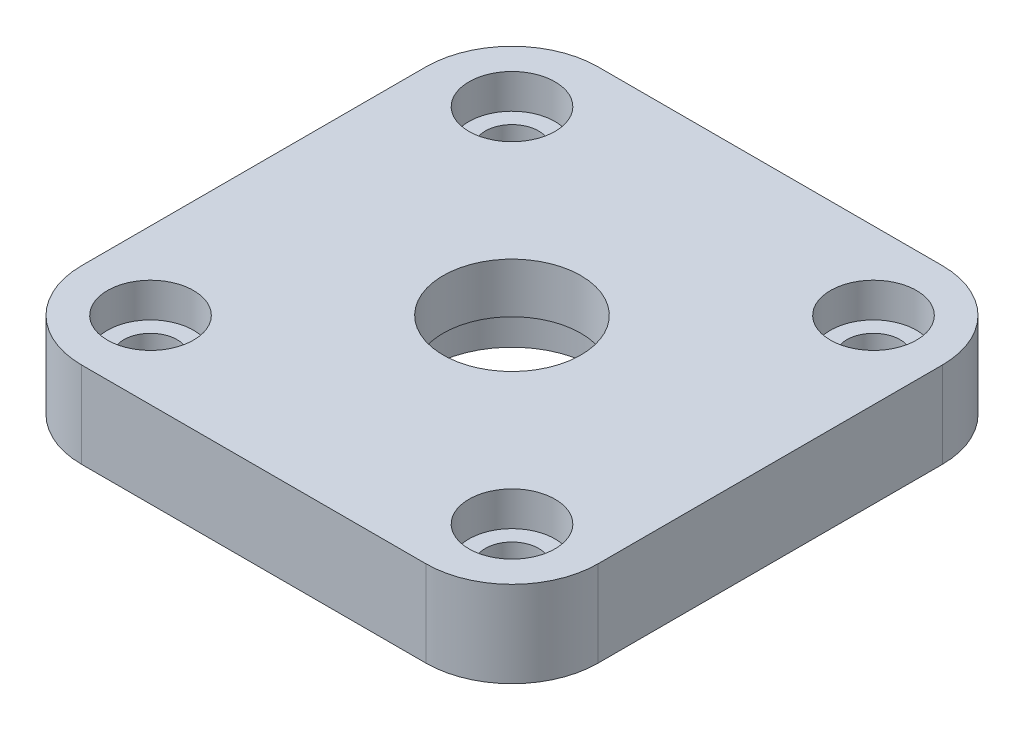
SolidWorks part; units mm, degrees
ref_plane "Front Plane" through (0, 0, 0) normal (0, 0, 1) x (1, 0, 0)
ref_plane "Top Plane" through (0, 0, 0) normal (0, 1, 0) x (1, 0, 0)
ref_plane "Right Plane" through (0, 0, 0) normal (1, 0, 0) x (0, 0, -1)
sketch "Sketch1" plane through (0, 0, 0) normal (0, 1, 0) x (1, 0, 0)
  line L1 (-15, -15) -> (15, -15)
  line L2 (-15, -15) -> (-15, 15)
  line L3 (-15, 15) -> (15, 15)
  line L4 (15, -15) -> (15, 15)
  line L5 (-15, -15) -> (15, 15) construction
  line L6 (-15, 15) -> (15, -15) construction
  point P0 (0, 0)
  dimension "D1" = 30
  dimension "D2" = 30
extrude "Boss-Extrude1" add sketch "Sketch1" along normal blind 5
sketch "Sketch2" plane through (0, 5, 0) normal (0, 1, 0) x (1, 0, 0)
  circle A0 centre (0, 0) radius 4
  dimension "D1" = 8
extrude "Cut-Extrude1" cut sketch "Sketch2" against normal through all both and the other way through all
sketch "Sketch3" plane through (0, 5, 0) normal (0, 1, 0) x (1, 0, 0)
  line L0 (-1000.6775, 10.5) -> (48999.3225, 10.5) construction
  line L1 (-1000.5978, -10.5) -> (48999.4022, -10.5) construction
  line L2 (-10.5, -999.6015) -> (-10.5, 49000.3985) construction
  line L3 (10.5, -999.5218) -> (10.5, 49000.4782) construction
  line L4 (-15, 15) -> (-15, -15) construction
  line L5 (15, 15) -> (-15, 15) construction
  line L7 (15, -15) -> (15, 15) construction
  line L8 (-15, -15) -> (15, -15) construction
  circle A0 centre (-10.5, 10.5) radius 1.55
  circle A1 centre (10.5, 10.5) radius 1.55
  circle A2 centre (10.5, -10.5) radius 1.55
  circle A3 centre (-10.5, -10.5) radius 1.55
  dimension "D6" = 3.1
  dimension "D8" = 3.1
  dimension "D10" = 3.1
  dimension "D12" = 3.1
  dimension "D1" = 4.5
  dimension "D2" = 4.5
  dimension "D3" = 4.5
  dimension "D4" = 4.5
  dimension "D5" = 0
  dimension "D7" = 0
  dimension "D9" = 0
  dimension "D11" = 0
extrude "Cut-Extrude2" cut sketch "Sketch3" against normal through all both and the other way through all
sketch "Sketch4" plane through (0, 0, 0) normal (0, -1, 0) x (1, 0, 0)
  circle A0 centre (0, 0) radius 4.8
  dimension "D1" = 9.6
extrude "Cut-Extrude3" cut sketch "Sketch4" against normal blind 2.1
fillet "Fillet1" radius 5 4 edges at (-15, 2.5, 15) (-15, 2.5, -15) (15, 2.5, -15) (15, 2.5, 15)
sketch "Sketch5" plane through (0, 5, 0) normal (0, 1, 0) x (1, 0, 0)
  circle A0 centre (-10.5, 10.5) radius 2.5
  circle A1 centre (10.5, 10.5) radius 2.5
  circle A2 centre (-10.5, -10.5) radius 2.5
  circle A3 centre (10.5, -10.5) radius 2.5
  dimension "D1" = 5
  dimension "D2" = 5
  dimension "D3" = 5
  dimension "D4" = 5
extrude "Cut-Extrude4" cut sketch "Sketch5" against normal blind 2
